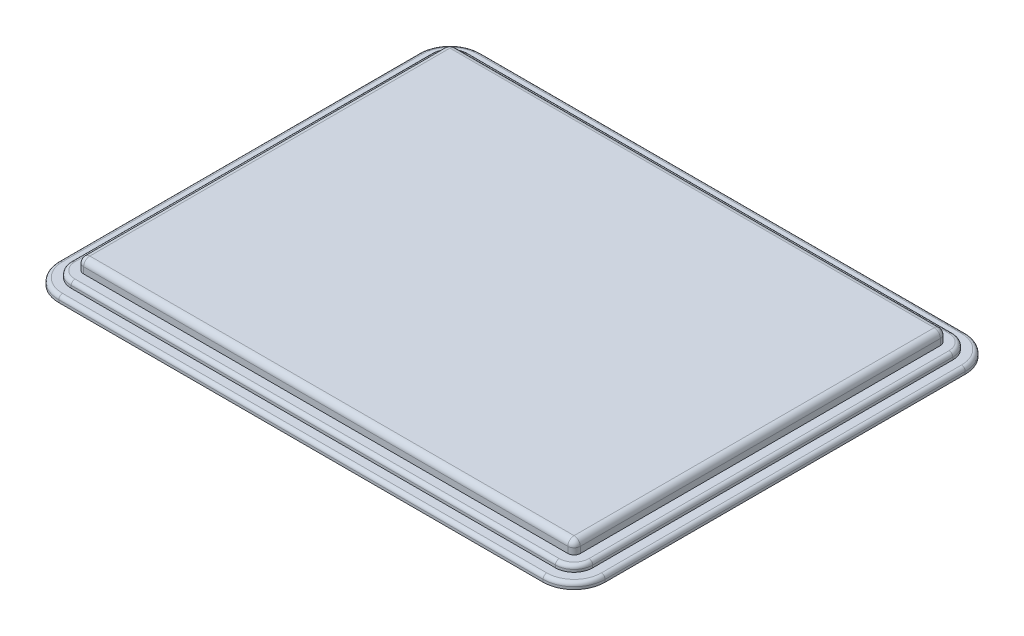
SolidWorks part; units mm, degrees
ref_plane "Front Plane" through (0, 0, 0) normal (0, 0, 1) x (1, 0, 0)
ref_plane "Top Plane" through (0, 0, 0) normal (0, 1, 0) x (1, 0, 0)
ref_plane "Right Plane" through (0, 0, 0) normal (1, 0, 0) x (0, 0, -1)
sketch "Sketch1" plane through (0, 0, 0) normal (0, 1, 0) x (1, 0, 0)
  line L1 (-195, -150) -> (195, -150)
  line L2 (-200, -145) -> (-200, 145)
  line L3 (-195, 150) -> (195, 150)
  line L4 (200, -145) -> (200, 145)
  line L5 (-200, -150) -> (200, 150) construction
  line L6 (-200, 150) -> (200, -150) construction
  arc A0 (-195, -150) -> (-200, -145) centre (-195, -145) cw
  arc A1 (195, -150) -> (200, -145) centre (195, -145) ccw
  arc A2 (195, 150) -> (200, 145) centre (195, 145) cw
  arc A3 (-200, 145) -> (-195, 150) centre (-195, 145) cw
  point P0 (0, 0)
  dimension "D3" = 5
  dimension "D1" = 400
  dimension "D2" = 300
extrude "Boss-Extrude1" add sketch "Sketch1" along normal blind 10
fillet "Fillet1" radius 5 8 edges at (-200, 10, 0) (-198.5355, 10, -148.5355) (0, 10, -150) (198.5355, 10, -148.5355) (200, 10, 0) (198.5355, 10, 148.5355) (0, 10, 150) (-198.5355, 10, 148.5355)
sketch "Sketch4" plane through (0, 0, 0) normal (0, -1, 0) x (1, 0, 0)
  line L8 (-210, 145) -> (-210, -145)
  line L9 (-195, -160) -> (195, -160)
  line L10 (210, -145) -> (210, 145)
  line L11 (195, 160) -> (-195, 160)
  line L12 (-210, 145) -> (-210, -145)
  line L13 (-195, -160) -> (195, -160)
  line L14 (210, -145) -> (210, 145)
  line L15 (195, 160) -> (-195, 160)
  arc A8 (-195, 160) -> (-210, 145) centre (-195, 145) ccw
  arc A9 (-210, -145) -> (-195, -160) centre (-195, -145) ccw
  arc A10 (195, -160) -> (210, -145) centre (195, -145) ccw
  arc A11 (210, 145) -> (195, 160) centre (195, 145) ccw
  arc A12 (-195, 160) -> (-210, 145) centre (-195, 145) ccw
  arc A13 (-210, -145) -> (-195, -160) centre (-195, -145) ccw
  arc A14 (195, -160) -> (210, -145) centre (195, -145) ccw
  arc A15 (210, 145) -> (195, 160) centre (195, 145) ccw
  dimension "D1" = 10
extrude "Boss-Extrude2" add sketch "Sketch4" along normal blind 5 separate body contours L14 A15 L15 A12 L12 A13 L13 A14
sketch "Sketch5" plane through (0, -5, 0) normal (0, -1, 0) x (1, 0, 0)
  line L8 (-220, 145) -> (-220, -145)
  line L9 (-195, -170) -> (195, -170)
  line L10 (220, -145) -> (220, 145)
  line L11 (195, 170) -> (-195, 170)
  line L12 (-220, 145) -> (-220, -145)
  line L13 (-195, -170) -> (195, -170)
  line L14 (220, -145) -> (220, 145)
  line L15 (195, 170) -> (-195, 170)
  arc A8 (-195, 170) -> (-220, 145) centre (-195, 145) ccw
  arc A9 (-220, -145) -> (-195, -170) centre (-195, -145) ccw
  arc A10 (195, -170) -> (220, -145) centre (195, -145) ccw
  arc A11 (220, 145) -> (195, 170) centre (195, 145) ccw
  arc A12 (-195, 170) -> (-220, 145) centre (-195, 145) ccw
  arc A13 (-220, -145) -> (-195, -170) centre (-195, -145) ccw
  arc A14 (195, -170) -> (220, -145) centre (195, -145) ccw
  arc A15 (220, 145) -> (195, 170) centre (195, 145) ccw
  dimension "D1" = 10
extrude "Boss-Extrude3" add sketch "Sketch5" along normal blind 5 contours L15 A12 L12 A13 L13 A14 L14 A15
fillet "Fillet2" radius 3 16 edges at (0, -5, 170) (212.6777, -5, 162.6777) (220, -5, 0) (212.6777, -5, -162.6777) (0, -5, -170) (-212.6777, -5, -162.6777) (-220, -5, 0) (0, 0, 160) (205.6066, 0, 155.6066) (210, 0, 0) (205.6066, 0, -155.6066) (0, 0, -160) (-205.6066, 0, -155.6066) (-210, 0, 0) (-212.6777, -5, 162.6777) (-205.6066, 0, 155.6066)
